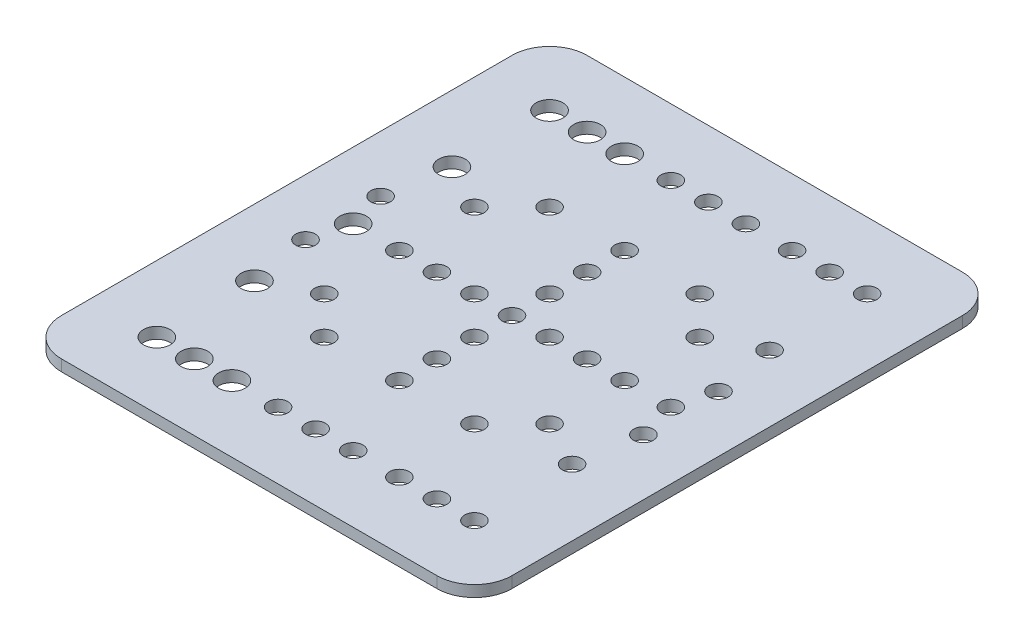
SolidWorks part; units mm, degrees
material "6061-T6 (SS)"
ref_plane "Front Plane" through (0, 0, 0) normal (0, 0, 1) x (1, 0, 0)
ref_plane "Top Plane" through (0, 0, 0) normal (0, 1, 0) x (1, 0, 0)
ref_plane "Right Plane" through (0, 0, 0) normal (1, 0, 0) x (0, 0, -1)
sketch "Sketch1" plane through (0, 0, 0) normal (0, 1, 0) x (1, 0, 0)
  line L0 (0, 0) -> (60, 0) construction
  line L1 (50, -70) -> (-50, -70)
  line L2 (60, -60) -> (60, 60)
  line L3 (50, 70) -> (-50, 70)
  line L4 (-60, -60) -> (-60, 60)
  line L5 (0, 70) -> (0, 0) construction
  arc A0 (-50, -70) -> (-60, -60) centre (-50, -60) cw
  arc A1 (50, -70) -> (60, -60) centre (50, -60) ccw
  arc A2 (60, 60) -> (50, 70) centre (50, 60) ccw
  arc A3 (-50, 70) -> (-60, 60) centre (-50, 60) ccw
  circle A4 centre (-32.3, 52.3) radius 3.55
  circle A5 centre (0, 10) radius 2.6
  circle A6 centre (0, 0) radius 2.6
  circle A7 centre (10, 0) radius 2.6
  circle A8 centre (-10, 0) radius 2.6
  circle A9 centre (-42.3, 52.3) radius 3.55
  circle A10 centre (-42.3, 0) radius 3.55
  circle A11 centre (-42.3, -52.3) radius 3.55
  circle A12 centre (-30, 20) radius 2.6
  circle A13 centre (-45, 10) radius 2.6
  circle A14 centre (-20, 30) radius 2.6
  circle A15 centre (0, 20) radius 2.6
  circle A16 centre (-10, 52.3) radius 2.6
  circle A17 centre (0, 52.3) radius 2.6
  circle A18 centre (10, 52.3) radius 2.6
  circle A19 centre (0, 30) radius 2.6
  circle A20 centre (20, 30) radius 2.6
  circle A21 centre (30, 20) radius 2.6
  circle A22 centre (45, 10) radius 2.6
  circle A23 centre (32.3, 52.3) radius 2.6
  circle A24 centre (42.3, 52.3) radius 2.6
  circle A25 centre (42.3, 0) radius 2.6
  circle A26 centre (45, -10) radius 2.6
  circle A27 centre (42.3, -52.3) radius 2.6
  circle A28 centre (32.3, -52.3) radius 2.6
  circle A29 centre (30, -20) radius 2.6
  circle A30 centre (0, -10) radius 2.6
  circle A31 centre (20, -30) radius 2.6
  circle A32 centre (20, 0) radius 2.6
  circle A33 centre (10, -52.3) radius 2.6
  circle A34 centre (0, -52.3) radius 2.6
  circle A35 centre (-10, -52.3) radius 2.6
  circle A36 centre (30, 0) radius 2.6
  circle A37 centre (-20, -30) radius 2.6
  circle A38 centre (-30, -20) radius 2.6
  circle A39 centre (-45, -10) radius 2.6
  circle A40 centre (-32.3, -52.3) radius 3.55
  circle A41 centre (-22.3, 52.3) radius 3.55
  circle A42 centre (22.3, 52.3) radius 2.6
  circle A43 centre (-20, 0) radius 2.6
  circle A44 centre (-30, 0) radius 2.6
  circle A45 centre (-42.3, 26.3) radius 3.55
  circle A46 centre (22.3, -52.3) radius 2.6
  circle A47 centre (-22.3, -52.3) radius 3.55
  circle A48 centre (-42.3, -26.3) radius 3.55
  circle A49 centre (42.3, 26.3) radius 2.6
  circle A50 centre (42.3, -26.3) radius 2.6
  circle A51 centre (0, -30) radius 2.6
  circle A52 centre (0, -20) radius 2.6
  point P0 (0, 0)
  dimension "D2" = 10
  dimension "D3" = 5.2
  dimension "D5" = 7.1
  dimension "D7" = 10
  dimension "D10" = 10
  dimension "D19" = 10
  dimension "D1" = 140
  dimension "D4" = 10
  dimension "D6" = 104.6
  dimension "D8" = 17.7
  dimension "D9" = 120
  dimension "D11" = 10
  dimension "D12" = 10
  dimension "D13" = 26
  dimension "D14" = 10
  dimension "D15" = 10
  dimension "D16" = 84.6
  dimension "D17" = 10
  dimension "D18" = 10
  dimension "D20" = 10
  dimension "D21" = 45
extrude "Boss-Extrude1" add sketch "Sketch1" along normal blind 3
